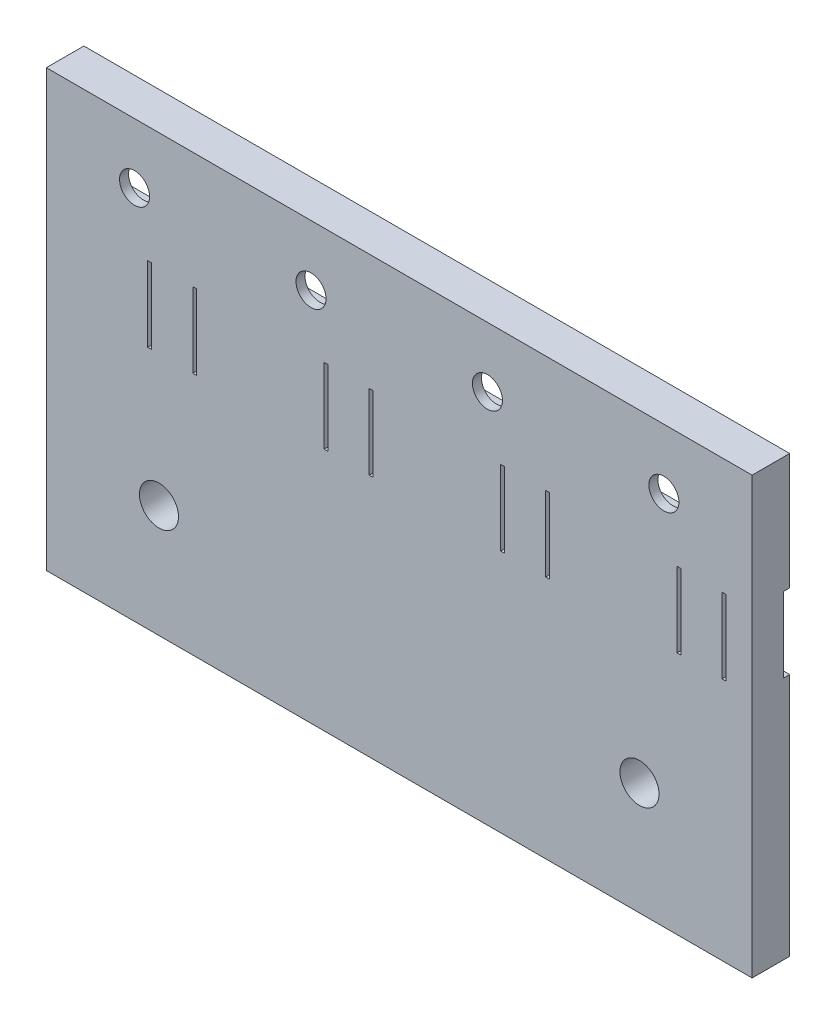
SolidWorks part; units mm, degrees
ref_plane "前视基准面" through (0, 0, 0) normal (0, 0, 1) x (1, 0, 0)
ref_plane "上视基准面" through (0, 0, 0) normal (0, 1, 0) x (1, 0, 0)
ref_plane "右视基准面" through (0, 0, 0) normal (1, 0, 0) x (0, 0, -1)
other "Configuration Table"
sketch "草图1" plane through (0, 0, 0) normal (0, 0, 1) x (1, 0, 0)
  line L0 (-0.5064, -0.9493) -> (93.4936, -0.9493)
  line L1 (-0.5064, 27.0507) -> (93.4936, 27.0507)
  line L2 (-0.5064, 27.0507) -> (-0.5064, -30.9493)
  line L3 (-0.5064, -30.9493) -> (93.4936, -30.9493)
  line L4 (93.4936, 27.0507) -> (93.4936, -30.9493)
  line L5 (46.4936, 27.0507) -> (46.4936, -30.9493) construction
  line L6 (-0.5064, -15.9493) -> (93.4936, -15.9493) construction
  line L7 (1.2436, 24.0507) -> (21.2436, 24.0507) construction
  line L8 (71.7436, 24.0507) -> (91.7436, 24.0507) construction
  line L9 (71.7436, 24.0507) -> (71.7436, 14.0507) construction
  line L10 (71.7436, 14.0507) -> (91.7436, 14.0507) construction
  line L11 (91.7436, 24.0507) -> (91.7436, 14.0507) construction
  line L24 (1.2436, 24.0507) -> (1.2436, 14.0507) construction
  line L25 (1.2436, 14.0507) -> (21.2436, 14.0507) construction
  line L26 (21.2436, 24.0507) -> (21.2436, 14.0507) construction
  line L27 (24.7436, 23.9652) -> (44.7436, 23.9652) construction
  line L28 (24.7436, 23.9652) -> (24.7436, 14.0507) construction
  line L29 (24.7436, 14.0507) -> (44.7436, 14.0507) construction
  line L30 (44.7436, 23.9652) -> (44.7436, 14.0507) construction
  line L31 (48.2436, 24.0072) -> (68.2436, 24.0072) construction
  line L32 (48.2436, 24.0072) -> (48.2436, 14.0507) construction
  line L33 (48.2436, 14.0507) -> (68.2436, 14.0507) construction
  line L34 (68.2436, 24.0072) -> (68.2436, 14.0507) construction
  line L35 (91.7436, 14.0507) -> (-0.5064, 14.0507) construction
  line L36 (1.2436, 24.0507) -> (21.2436, 14.0507) construction
  line L37 (24.7436, 23.9652) -> (44.7436, 14.0507) construction
  line L38 (48.2436, 24.0072) -> (68.2436, 14.0507) construction
  line L39 (71.7436, 24.0507) -> (91.7436, 14.0507) construction
  circle A0 centre (14.4936, -15.9493) radius 2.6
  circle A1 centre (78.4936, -15.9493) radius 2.6
  circle A2 centre (11.2436, 19.0507) radius 2
  circle A3 centre (34.7436, 19.0079) radius 2
  circle A4 centre (58.2436, 19.0289) radius 2
  circle A5 centre (81.7436, 19.0507) radius 2
  dimension "D5" = 5.2
  dimension "D18" = 4
  dimension "D1" = 94
  dimension "D2" = 58
  dimension "D3" = 30
  dimension "D4" = 15
  dimension "D6" = 15
  dimension "D7" = 3
  dimension "D8" = 20
  dimension "D9" = 10
  dimension "D10" = 1.75
  dimension "D11" = 3.5
  dimension "D12" = 20
  dimension "D13" = 20
  dimension "D14" = 20
  dimension "D15" = 3.5
  dimension "D16" = 3.5
  dimension "D17" = 1.75
extrude "凸台-拉伸1" add sketch "草图1" along normal blind 5 contours L4 L1 L2 L0 A5 A4 A3 A2 | L4 L0 L2 L3 A0 A1
sketch "草图2" plane through (0, 0, 0) normal (0, 0, -1) x (-1, 0, 0)
  line L1 (-91.7436, 24.0507) -> (-71.7436, 24.0507)
  line L2 (-91.7436, 24.0507) -> (-91.7436, 14.0507)
  line L3 (-91.7436, 14.0507) -> (-71.7436, 14.0507)
  line L4 (-71.7436, 24.0507) -> (-71.7436, 14.0507)
  line L5 (-68.2436, 24.0072) -> (-48.2436, 24.0072)
  line L6 (-68.2436, 24.0072) -> (-68.2436, 14.0507)
  line L7 (-68.2436, 14.0507) -> (-48.2436, 14.0507)
  line L8 (-48.2436, 24.0072) -> (-48.2436, 14.0507)
  line L9 (-44.7436, 23.9652) -> (-24.7436, 23.9652)
  line L10 (-44.7436, 23.9652) -> (-44.7436, 14.0507)
  line L11 (-44.7436, 14.0507) -> (-24.7436, 14.0507)
  line L12 (-24.7436, 23.9652) -> (-24.7436, 14.0507)
  line L13 (-21.2436, 24.0507) -> (-1.2436, 24.0507)
  line L14 (-21.2436, 24.0507) -> (-21.2436, 14.0507)
  line L15 (-21.2436, 14.0507) -> (-1.2436, 14.0507)
  line L16 (-1.2436, 24.0507) -> (-1.2436, 14.0507)
extrude "切除-拉伸1" cut sketch "草图2" against normal blind 3.8
sketch "草图3" plane through (0, 0, 0) normal (0, 0, -1) x (-1, 0, 0)
  line L0 (-81.7436, 14.0507) -> (-81.7436, -0.9493) construction
  line L1 (-13.4936, 11.5507) -> (4.5064, 11.5507)
  line L2 (-13.4936, 11.5507) -> (-13.4936, 1.5507)
  line L3 (-13.4936, 1.5507) -> (4.5064, 1.5507)
  line L4 (4.5064, 11.5507) -> (4.5064, 1.5507)
  line L5 (-71.7436, 14.0507) -> (-91.7436, 14.0507) construction
  line L6 (0.5064, -0.9493) -> (-93.4936, -0.9493) construction
  line L7 (-81.7436, 6.5507) -> (0.5064, 6.5507) construction
  line L8 (0.5064, 27.0507) -> (0.5064, -30.9493) construction
  line L9 (-36.9936, 11.5507) -> (-18.9936, 11.5507)
  line L10 (-36.9936, 11.5507) -> (-36.9936, 1.5507)
  line L11 (-36.9936, 1.5507) -> (-18.9936, 1.5507)
  line L12 (-18.9936, 11.5507) -> (-18.9936, 1.5507)
  line L13 (-60.4936, 11.5507) -> (-42.4936, 11.5507)
  line L14 (-60.4936, 11.5507) -> (-60.4936, 1.5507)
  line L15 (-60.4936, 1.5507) -> (-42.4936, 1.5507)
  line L16 (-42.4936, 11.5507) -> (-42.4936, 1.5507)
  line L21 (-83.9936, 11.5507) -> (-65.9936, 11.5507)
  line L22 (-83.9936, 11.5507) -> (-83.9936, 1.5507)
  line L23 (-83.9936, 1.5507) -> (-65.9936, 1.5507)
  line L24 (-65.9936, 11.5507) -> (-65.9936, 1.5507)
  line L25 (-107.4936, 11.5507) -> (-89.4936, 11.5507)
  line L26 (-107.4936, 11.5507) -> (-107.4936, 1.5507)
  line L27 (-107.4936, 1.5507) -> (-89.4936, 1.5507)
  line L28 (-89.4936, 11.5507) -> (-89.4936, 1.5507)
  line L29 (-93.4936, 27.0507) -> (-93.4936, -30.9493) construction
  point P14 (-13.4936, 6.5507)
  point P19 (-36.9936, 6.5507)
  point P24 (-60.4936, 6.5507)
  point P29 (-107.4936, 6.5507)
  point P34 (-83.9936, 6.5507)
  point P35 (-89.4936, 6.5507)
  dimension "D1" = 18
  dimension "D2" = 10
  dimension "D3" = 4
  dimension "D4" = 5.5
  dimension "D5" = 18
  dimension "D6" = 18
  dimension "D7" = 18
  dimension "D8" = 10
  dimension "D9" = 10
  dimension "D10" = 10
  dimension "D11" = 5.5
  dimension "D12" = 5.5
  dimension "D13" = 18
  dimension "D14" = 10
  dimension "D15" = 5.5
  dimension "D16" = 4
extrude "切除-拉伸2" cut sketch "草图3" against normal blind 0.8
sketch "草图4" plane through (0, 0, 0) normal (0, 0, -1) x (-1, 0, 0)
  line L0 (-13.4936, 1.5507) -> (0.5064, 1.5507) construction
  line L1 (-13.4936, 11.5507) -> (-12.9936, 11.5507)
  line L2 (-13.4936, 11.5507) -> (-13.4936, 1.5507)
  line L3 (-13.4936, 1.5507) -> (-12.9936, 1.5507)
  line L4 (-12.9936, 11.5507) -> (-12.9936, 1.5507)
  line L5 (-36.9936, 1.5507) -> (-18.9936, 1.5507) construction
  line L6 (-18.9936, 11.5507) -> (-19.4936, 11.5507)
  line L7 (-18.9936, 11.5507) -> (-18.9936, 1.5507)
  line L8 (-18.9936, 1.5507) -> (-19.4936, 1.5507)
  line L9 (-19.4936, 11.5507) -> (-19.4936, 1.5507)
  line L10 (-18.9936, 11.5507) -> (-36.9936, 11.5507) construction
  line L11 (-36.9936, 1.5507) -> (-36.4936, 1.5507)
  line L12 (-36.9936, 1.5507) -> (-36.9936, 11.5507)
  line L13 (-36.9936, 11.5507) -> (-36.4936, 11.5507)
  line L14 (-36.4936, 1.5507) -> (-36.4936, 11.5507)
  line L15 (-60.4936, 1.5507) -> (-42.4936, 1.5507) construction
  line L16 (-42.4936, 11.5507) -> (-42.9936, 11.5507)
  line L17 (-42.4936, 11.5507) -> (-42.4936, 1.5507)
  line L18 (-42.4936, 1.5507) -> (-42.9936, 1.5507)
  line L19 (-42.9936, 11.5507) -> (-42.9936, 1.5507)
  line L20 (-83.9936, 1.5507) -> (-65.9936, 1.5507) construction
  line L21 (-60.4936, 11.5507) -> (-59.9936, 11.5507)
  line L22 (-60.4936, 11.5507) -> (-60.4936, 1.5507)
  line L23 (-60.4936, 1.5507) -> (-59.9936, 1.5507)
  line L24 (-59.9936, 11.5507) -> (-59.9936, 1.5507)
  line L25 (-65.9936, 11.5507) -> (-66.4936, 11.5507)
  line L26 (-65.9936, 11.5507) -> (-65.9936, 1.5507)
  line L27 (-65.9936, 1.5507) -> (-66.4936, 1.5507)
  line L28 (-66.4936, 11.5507) -> (-66.4936, 1.5507)
  line L29 (-83.9936, 1.5507) -> (-65.9936, 1.5507) construction
  line L30 (-83.9936, 11.5507) -> (-83.4936, 11.5507)
  line L31 (-83.9936, 11.5507) -> (-83.9936, 1.5507)
  line L32 (-83.9936, 1.5507) -> (-83.4936, 1.5507)
  line L33 (-83.4936, 11.5507) -> (-83.4936, 1.5507)
  line L34 (-89.4936, 1.5507) -> (-93.4936, 1.5507) construction
  line L35 (-89.4936, 11.5507) -> (-89.9936, 11.5507)
  line L36 (-89.4936, 11.5507) -> (-89.4936, 1.5507)
  line L37 (-89.4936, 1.5507) -> (-89.9936, 1.5507)
  line L38 (-89.9936, 11.5507) -> (-89.9936, 1.5507)
  dimension "D1" = 0.5
extrude "切除-拉伸3" cut sketch "草图4" against normal through all
sketch "草图6" plane through (0, 0, 5) normal (0, 0, 1) x (1, 0, 0)
  line L0 (12.9936, 1.5507) -> (12.9936, 11.5507) construction
  line L1 (12.9936, 9.1713) -> (9.792, 9.1713)
  line L2 (12.9936, 9.1713) -> (12.9936, 3.4501)
  line L3 (12.9936, 3.4501) -> (9.792, 3.4501)
  line L4 (9.792, 9.1713) -> (9.792, 3.4501)
